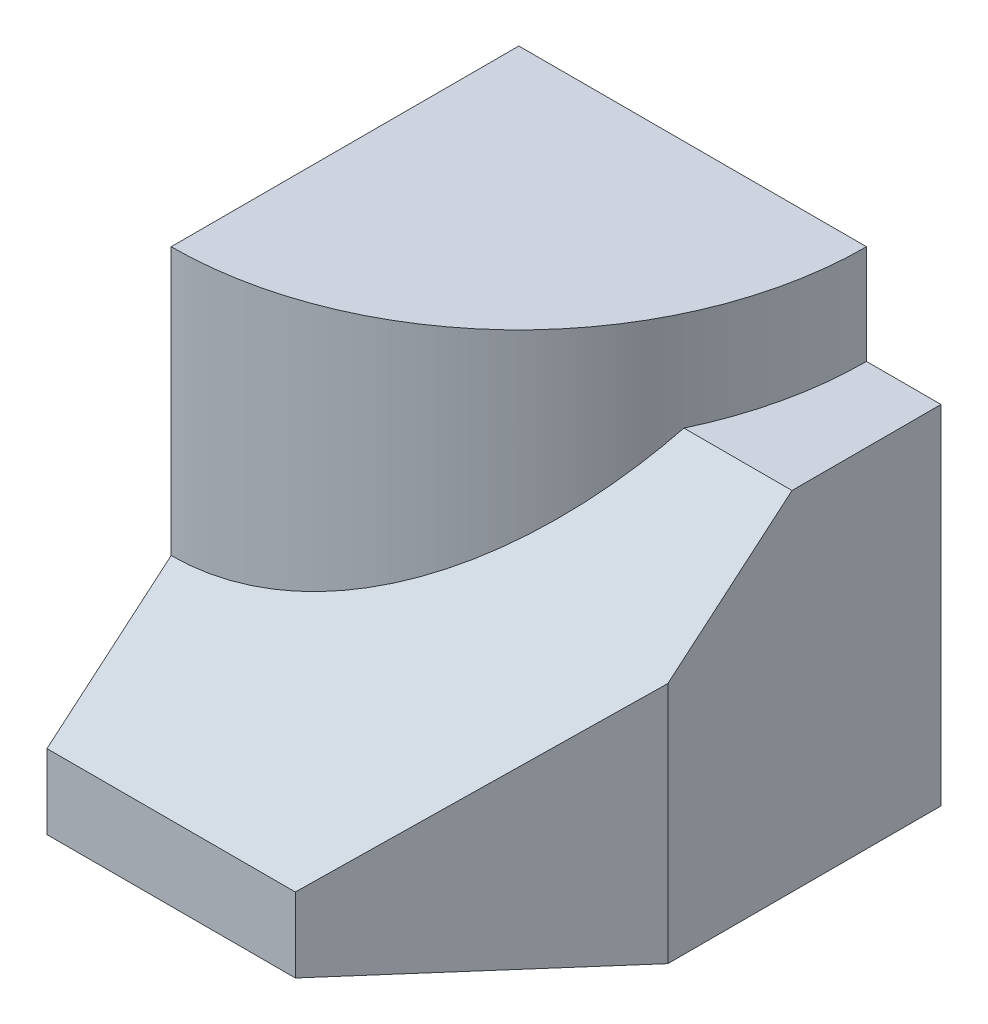
SolidWorks part; units mm, degrees
ref_plane "Front Plane" through (0, 0, 0) normal (0, 0, 1) x (1, 0, 0)
ref_plane "Top Plane" through (0, 0, 0) normal (0, 1, 0) x (1, 0, 0)
ref_plane "Right Plane" through (0, 0, 0) normal (1, 0, 0) x (0, 0, -1)
sketch "Sketch1" plane through (0, 0, 0) normal (0, 1, 0) x (1, 0, 0)
  line L0 (70, 0) -> (0, 0)
  line L1 (0, 0) -> (0, -70)
  arc A0 (0, -70) -> (70, 0) centre (0, 0) ccw
  dimension "D1" = 70
extrude "Extrude1" add sketch "Sketch1" along normal blind 90
sketch "Sketch2" plane through (0, 0, 0) normal (-1, 0, 0) x (0, 0, 1)
  line L0 (0, 70) -> (30, 70)
  line L1 (0, 90) -> (0, 0) construction
  line L2 (30, 70) -> (95, 15)
  line L3 (95, 15) -> (95, 0)
  line L4 (95, 0) -> (0, 0)
  line L5 (0, 0) -> (0, 70)
  dimension "D1" = 30
  dimension "D2" = 95
  dimension "D3" = 15
  dimension "D4" = 70
extrude "Extrude2" add sketch "Sketch2" against normal blind 85
sketch "Sketch3" plane through (0, 0, 0) normal (0, 1, 0) x (1, 0, 0)
  line L0 (85, -55) -> (50, -95)
  line L1 (85, 0) -> (85, -95) construction
  line L2 (85, -95) -> (0, -95) construction
  line L3 (50, -95) -> (85, -95)
  line L4 (85, -95) -> (85, -55)
  dimension "D1" = 50
  dimension "D2" = 55
extrude "Extrude3" cut sketch "Sketch3" along normal through all
